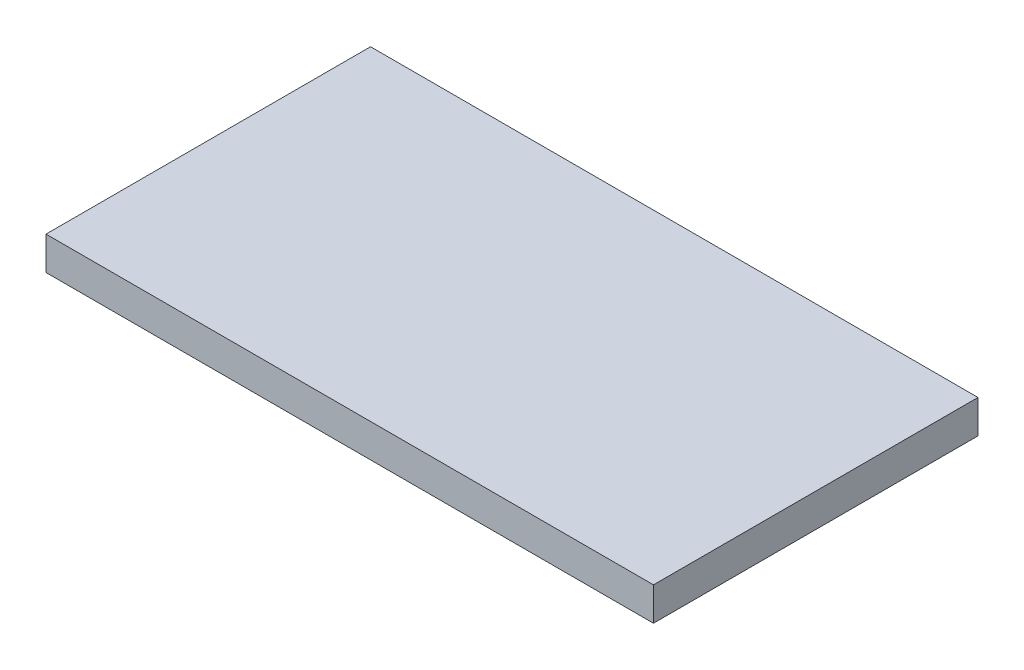
SolidWorks part; units mm, degrees
ref_plane "Plano frontal" through (0, 0, 0) normal (0, 0, 1) x (1, 0, 0)
ref_plane "Plano superior" through (0, 0, 0) normal (0, 1, 0) x (1, 0, 0)
ref_plane "Plano direito" through (0, 0, 0) normal (1, 0, 0) x (0, 0, -1)
sketch "Esboço1" plane through (0, 0, 0) normal (0, 1, 0) x (1, 0, 0)
  line L1 (-18.25, -9.75) -> (18.25, -9.75)
  line L2 (-18.25, -9.75) -> (-18.25, 9.75)
  line L3 (-18.25, 9.75) -> (18.25, 9.75)
  line L4 (18.25, -9.75) -> (18.25, 9.75)
  line L5 (-18.25, -9.75) -> (18.25, 9.75) construction
  line L6 (-18.25, 9.75) -> (18.25, -9.75) construction
  point P0 (0, 0)
  dimension "D1" = 19.5
  dimension "D2" = 36.5
extrude "Ressalto-extrusão1" add sketch "Esboço1" along normal blind 2
